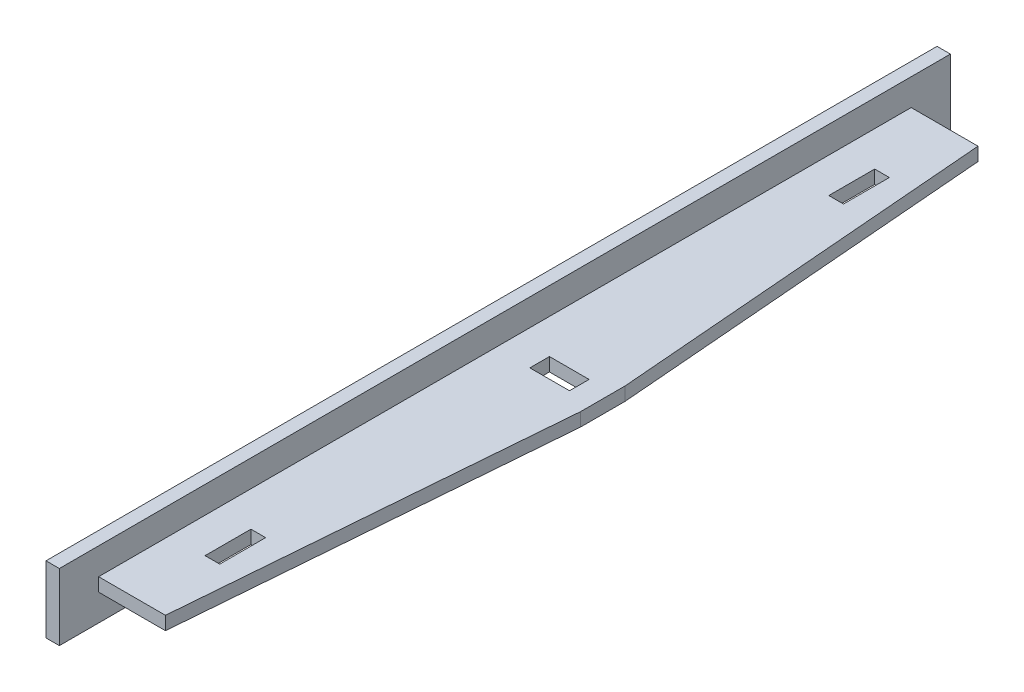
SolidWorks part; units mm, degrees
ref_plane "前视基准面" through (0, 0, 0) normal (0, 0, 1) x (1, 0, 0)
ref_plane "上视基准面" through (0, 0, 0) normal (0, 1, 0) x (1, 0, 0)
ref_plane "右视基准面" through (0, 0, 0) normal (1, 0, 0) x (0, 0, -1)
other "Configuration Table"
sketch "草图1" plane through (0, 0, 0) normal (0, 0, 1) x (1, 0, 0)
  line L1 (0, 0) -> (3, 0)
  line L2 (0, 0) -> (0, 15)
  line L3 (0, 15) -> (3, 15)
  line L4 (3, 0) -> (3, 15)
  dimension "D1" = 15
  dimension "D2" = 3
extrude "凸台-拉伸1" add sketch "草图1" along normal blind 200
ref_plane "基准面1" through (0, 9, 0) normal (0, 1, 0) x (1, 0, 0)
sketch "草图12" plane through (0, 9, 0) normal (0, 1, 0) x (1, 0, 0)
  line L0 (3, -100) -> (91.3211, -100) construction
  line L1 (18, -191.19) -> (25, -105)
  line L2 (3, -8.81) -> (18, -8.81)
  line L3 (3, -200) -> (3, 0) construction
  line L4 (18, -8.81) -> (25, -95)
  line L5 (25, -95) -> (25, -105)
  line L6 (3, -8.81) -> (3, -191.19)
  line L7 (3, -191.19) -> (18, -191.19)
  point P12 (3, -100)
  point P13 (25, -100)
  dimension "D1" = 5
  dimension "D2" = 22
  dimension "D3" = 15
  dimension "D4" = 8.81
extrude "凸台-拉伸7" add sketch "草图12" against normal blind 3
sketch "草图13" plane through (0, 6, 0) normal (0, -1, 0) x (1, 0, 0)
  line L0 (25.3456, 100) -> (-14.3456, 100) construction
  line L1 (10.8, 102.2) -> (19.7, 102.2)
  line L2 (10.8, 102.2) -> (10.8, 97.8)
  line L3 (10.8, 97.8) -> (19.7, 97.8)
  line L4 (19.7, 102.2) -> (19.7, 97.8)
  line L5 (10.8, 102.2) -> (19.7, 97.8) construction
  line L6 (10.8, 97.8) -> (19.7, 102.2) construction
  line L7 (19.5, 102) -> (19.5, 98) construction
  line L8 (11, 102) -> (11, 98) construction
  line L9 (19.5, 98) -> (11, 98) construction
  line L10 (14, 35) -> (14, 25) construction
  line L11 (10.85, 35.15) -> (14.15, 35.15)
  line L12 (10.85, 35.15) -> (10.85, 24.85)
  line L13 (10.85, 24.85) -> (14.15, 24.85)
  line L14 (14.15, 35.15) -> (14.15, 24.85)
  line L15 (10.85, 35.15) -> (14.15, 24.85) construction
  line L16 (10.85, 24.85) -> (14.15, 35.15) construction
  line L17 (14, 25) -> (11, 25) construction
  line L18 (10.85, 175.15) -> (14.15, 164.85) construction
  line L19 (10.85, 164.85) -> (14.15, 175.15) construction
  line L20 (14.15, 164.85) -> (14.15, 175.15)
  line L21 (10.85, 175.15) -> (14.15, 175.15)
  line L22 (10.85, 164.85) -> (10.85, 175.15)
  line L23 (10.85, 164.85) -> (14.15, 164.85)
  point P0 (15.25, 100)
  point P13 (12.5, 30)
  point P18 (0, 0)
  point P27 (12.5, 170)
  dimension "D1" = 0.2
  dimension "D2" = 0.2
  dimension "D3" = 0.2
  dimension "D4" = 0.15
  dimension "D5" = 0.15
extrude "切除-拉伸1" cut sketch "草图13" against normal blind 10 contours L14 L11 L12 L13 | L22 L23 L20 L21 | L3 L4 L1 L2
